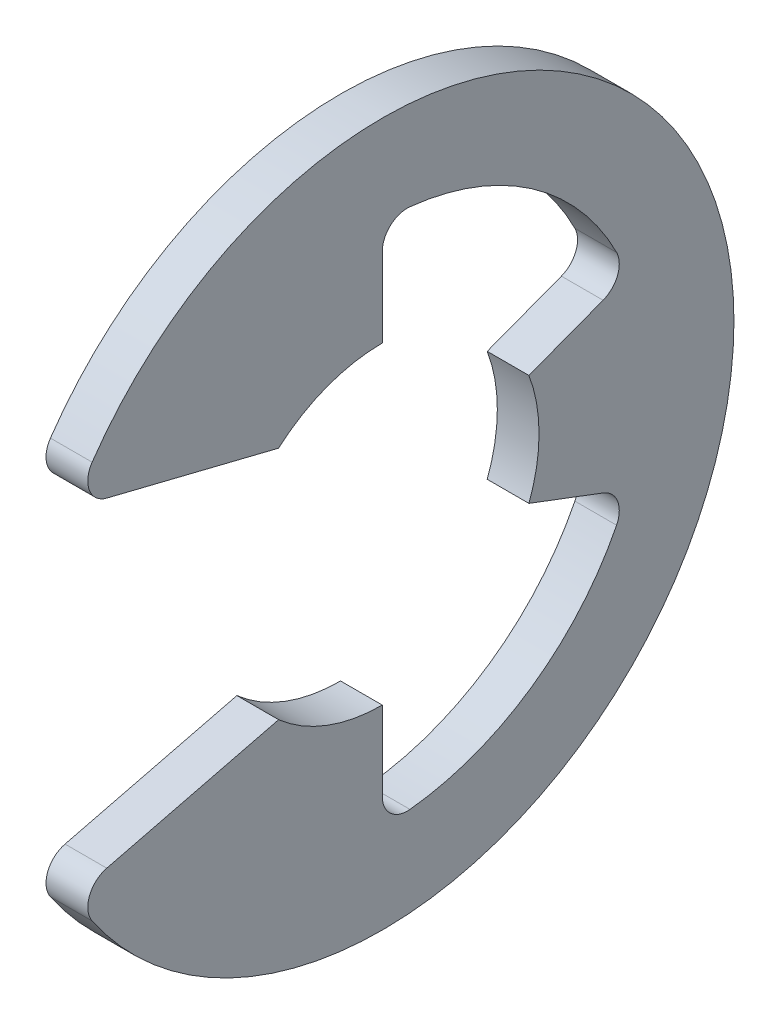
SolidWorks part; units mm, degrees
ref_plane "Front" through (0, 0, 0) normal (0, 0, 1) x (1, 0, 0)
ref_plane "Top" through (0, 0, 0) normal (0, 1, 0) x (1, 0, 0)
ref_plane "Right" through (0, 0, 0) normal (1, 0, 0) x (0, 0, -1)
sketch "Sketch1" plane through (0, 0, 0) normal (1, 0, 0) x (0, 0, -1)
  line L0 (-5.179, -2.8264) -> (-1.7396, -1.9725)
  line L1 (-5.179, 2.8264) -> (-1.7396, 1.9725)
  line L2 (0, -2.63) -> (0, -4.4026)
  line L3 (0, 2.63) -> (0, 4.4026)
  line L4 (2.4601, -0.9298) -> (4.1182, -1.5565)
  line L5 (2.4601, 0.9298) -> (4.1182, 1.5565)
  line L6 (0, 0) -> (-6.15, 0) construction
  line L7 (2.4601, 0.9298) -> (2.4601, -0.9298) construction
  line L8 (0, -2.63) -> (-1.7396, -1.9725) construction
  circle A1 centre (0, 0) radius 6.15 construction
  circle A2 centre (0, 0) radius 2.63 construction
  arc A3 (-5.179, -2.8264) -> (-5.179, 2.8264) centre (0, 0) ccw
  arc A4 (-1.7396, -1.9725) -> (0, -2.63) centre (0, 0) ccw
  arc A5 (-1.7396, 1.9725) -> (0, 2.63) centre (0, 0) cw
  arc A6 (2.4601, 0.9298) -> (2.4601, -0.9298) centre (0, 0) cw
  arc A7 (0, -4.4026) -> (4.1182, -1.5565) centre (0, 0) ccw
  arc A8 (4.1182, 1.5565) -> (0, 4.4026) centre (0, 0) ccw
  dimension "D" = 5.26
  dimension "D1" = 4.4026
  dimension "OD" = 11.8
  dimension "D2" = 2.9905
  dimension "D3" = 3.945
extrude "Extrude1" add sketch "Sketch1" along normal mid plane 0.7
fillet "Fillet1" radius 0.42 6 edges at (0, -4.4026, 0) (0, 4.4026, 0) (0, -2.8264, 5.179) (0, 2.8264, 5.179) (0, -1.5565, -4.1182) (0, 1.5565, -4.1182)
sketch "Sketch3" plane through (0, 0, 0) normal (0, 1, 0) x (1, 0, 0)
  line L0 (0.37, 3.5) -> (0.37, 3)
  line L1 (0.37, 3) -> (-0.37, 3)
  line L2 (-0.37, 3) -> (-0.37, 3.5)
  line L3 (-0.37, 3.5) -> (-5.18, 3.5)
  line L4 (2.22, 0) -> (2.22, 3.25)
  line L5 (-5.18, 3.5) -> (-5.18, 0)
  line L6 (-5.18, 0) -> (2.22, 0)
  line L8 (2.22, 0) -> (2.22, 3.5) construction
  line L9 (2.22, 3.5) -> (0.37, 3.5) construction
  line L10 (2.22, 0) -> (17.2631, 0) construction
  line L11 (2.22, 3.25) -> (1.97, 3.5)
  line L12 (1.97, 3.5) -> (0.37, 3.5)
  point P2 (0, 3)
  point P5 (0.37, 3.25)
  dimension "D2" = 7.4
  dimension "D1" = 1.85
  dimension "D3" = 45
revolve "Revolve2" [suppressed] add sketch "Sketch3" angle 360 about L10
equation "\"D2@Sketch3\" = \"W@Sketch3\"*10"
equation "\"D1@Sketch3\" = \"D2@Sketch3\"/4"
equation "\"D1@Sketch1\" = (\"OD@Sketch1\"+\"D@Sketch1\")/3.875"
equation "\"D3@Sketch1\" = \"D@Sketch1\"*.75"
equation "\"D1@Fillet1\" = \"D1@Extrude1\"*.6"
